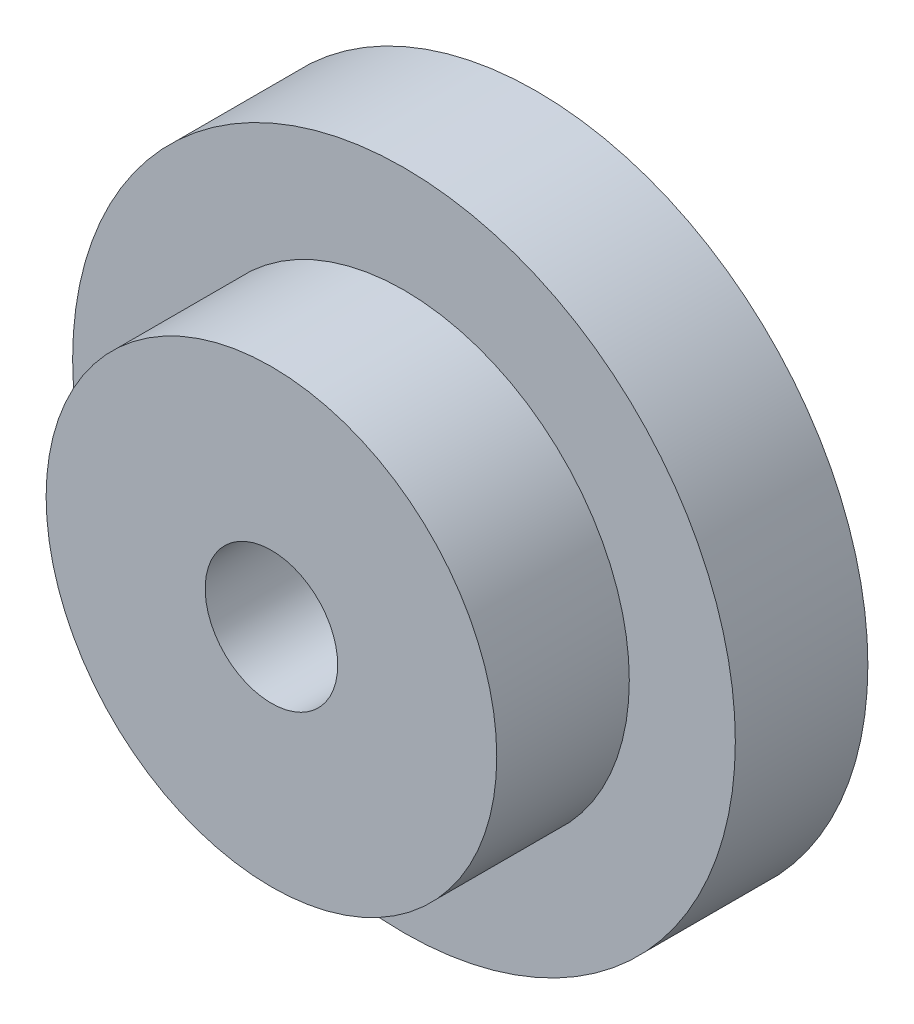
SolidWorks part; units mm, degrees
ref_plane "前视基准面" through (0, 0, 0) normal (0, 0, 1) x (1, 0, 0)
ref_plane "上视基准面" through (0, 0, 0) normal (0, 1, 0) x (1, 0, 0)
ref_plane "右视基准面" through (0, 0, 0) normal (1, 0, 0) x (0, 0, -1)
other "Configuration Table"
sketch "草图1" plane through (0, 0, 0) normal (0, 0, 1) x (1, 0, 0)
  circle A0 centre (0, 0) radius 2.5
  circle A1 centre (0, 0) radius 0.5
  dimension "D1" = 5
  dimension "D2" = 1
extrude "凸台-拉伸1" add sketch "草图1" along normal blind 1
sketch "草图2" plane through (0, 0, 1) normal (0, 0, 1) x (1, 0, 0)
  circle A0 centre (0, 0) radius 0.5 construction
  circle A1 centre (0, 0) radius 0.5
  circle A2 centre (0, 0) radius 1.7
  dimension "D1" = 3.4
extrude "凸台-拉伸2" add sketch "草图2" along normal blind 1
